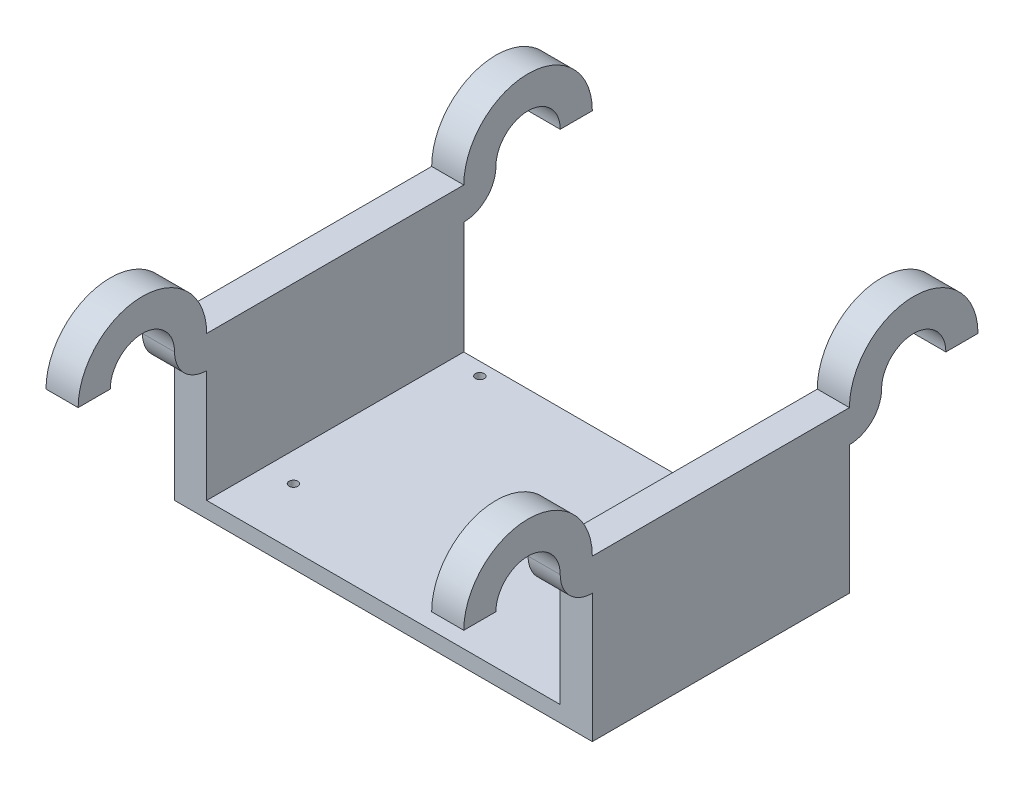
SolidWorks part; units mm, degrees
ref_plane "Front Plane" through (0, 0, 0) normal (0, 0, 1) x (1, 0, 0)
ref_plane "Top Plane" through (0, 0, 0) normal (0, 1, 0) x (1, 0, 0)
ref_plane "Right Plane" through (0, 0, 0) normal (1, 0, 0) x (0, 0, -1)
sketch "Sketch1" plane through (0, 0, 0) normal (0, 1, 0) x (1, 0, 0)
  line L1 (-65, -40) -> (65, -40)
  line L2 (-65, -40) -> (-65, 40)
  line L3 (-65, 40) -> (65, 40)
  line L4 (65, -40) -> (65, 40)
  line L5 (-65, -40) -> (65, 40) construction
  line L6 (-65, 40) -> (65, -40) construction
  point P0 (0, 0)
  dimension "D1" = 130
  dimension "D2" = 80
extrude "Boss-Extrude1" add sketch "Sketch1" along normal blind 5
sketch "Sketch2" plane through (0, 5, 0) normal (0, 1, 0) x (1, 0, 0)
  line L0 (-65, -40) -> (65, -40) construction
  line L1 (65, 40) -> (55, 40)
  line L2 (65, 40) -> (65, -40)
  line L3 (65, -40) -> (55, -40)
  line L4 (55, 40) -> (55, -40)
  line L5 (65, 40) -> (-65, 40) construction
  line L6 (-65, -40) -> (-55, -40)
  line L7 (-65, -40) -> (-65, 40)
  line L8 (-65, 40) -> (-55, 40)
  line L9 (-55, -40) -> (-55, 40)
  dimension "D1" = 10
  dimension "D2" = 10
extrude "Boss-Extrude2" add sketch "Sketch2" along normal blind 45
sketch "Sketch3" plane through (0, 5, 0) normal (0, 1, 0) x (1, 0, 0)
  circle A0 centre (-46, -22) radius 1.375 construction
  circle A1 centre (40, -22) radius 1.375 construction
  circle A2 centre (40, 36) radius 1.375 construction
  circle A3 centre (-46, 36) radius 1.375 construction
  circle A4 centre (-46, -22) radius 1.375
  circle A5 centre (40, -22) radius 1.375
  circle A6 centre (40, 36) radius 1.375
  circle A7 centre (-46, 36) radius 1.375
extrude "Cut-Extrude1" cut sketch "Sketch3" against normal through all both and the other way through all
sketch "Sketch4" plane through (-65, 0, 0) normal (-1, 0, 0) x (0, 0, 1)
  line L0 (0, 0) -> (0, 50) construction
  line L1 (-40, 50) -> (40, 50) construction
  line L2 (-60, 50) -> (60, 50) construction
  line L3 (-70, 50) -> (-40, 50)
  line L4 (70, 50) -> (40, 50)
  line L5 (-80, 50) -> (-70, 50)
  line L6 (80, 50) -> (70, 50)
  line L7 (-40, 50) -> (-40, 0) construction
  line L8 (40, 50) -> (40, 0) construction
  line L9 (-40, 50) -> (-40, 40)
  line L10 (40, 50) -> (40, 40)
  arc A0 (-50, 50) -> (-70, 50) centre (-60, 50) ccw
  arc A1 (70, 50) -> (50, 50) centre (60, 50) ccw
  arc A2 (-40, 50) -> (-80, 50) centre (-60, 50) ccw
  arc A3 (40, 50) -> (80, 50) centre (60, 50) cw
  arc A4 (-50, 50) -> (-40, 40) centre (-40, 50) ccw
  arc A5 (50, 50) -> (40, 40) centre (40, 50) cw
  point P3 (0, 50)
  line M3 (40, 0) -> (40, 50)
  line M5 (-40, 50) -> (-40, 0)
  dimension "D2" = 20
  dimension "D3" = 20
  dimension "D1" = 120
extrude "Boss-Extrude3" add sketch "Sketch4" against normal up to surface (10 mm away) contours L3 A2 L5 A0 | L3 A4 M5 | A3 L4 A1 L6 | A5 L4 M3 up to face at (-55, 27.5, 0)
sketch "Sketch5" plane through (65, 0, 0) normal (1, 0, 0) x (0, 0, -1)
  line L4 (-40, 0) -> (40, 0)
  line L5 (40, 0) -> (40, 50)
  line L6 (40, 50) -> (-40, 50)
  line L7 (-40, 50) -> (-40, 0)
  line L8 (-40, 0) -> (40, 0)
  line L9 (40, 0) -> (40, 50)
  line L10 (40, 50) -> (-40, 50)
  line L11 (-40, 50) -> (-40, 0)
  line L14 (-40, 5) -> (40, 5)
  line L15 (40, 5) -> (40, 40)
  line L16 (70, 50) -> (80, 50)
  line L17 (40, 50) -> (-40, 50)
  line L18 (-80, 50) -> (-70, 50)
  line L19 (-40, 40) -> (-40, 5)
  line L20 (-40, 5) -> (40, 5)
  line L21 (40, 5) -> (40, 40)
  line L22 (70, 50) -> (80, 50)
  line L23 (40, 50) -> (-40, 50)
  line L24 (-80, 50) -> (-70, 50)
  line L25 (-40, 40) -> (-40, 5)
  arc A6 (40, 40) -> (50, 50) centre (40, 50) ccw
  arc A7 (70, 50) -> (50, 50) centre (60, 50) ccw
  arc A8 (80, 50) -> (40, 50) centre (60, 50) ccw
  arc A9 (-40, 50) -> (-80, 50) centre (-60, 50) ccw
  arc A10 (-50, 50) -> (-70, 50) centre (-60, 50) ccw
  arc A11 (-50, 50) -> (-40, 40) centre (-40, 50) ccw
  arc A12 (40, 40) -> (50, 50) centre (40, 50) ccw
  arc A13 (70, 50) -> (50, 50) centre (60, 50) ccw
  arc A14 (80, 50) -> (40, 50) centre (60, 50) ccw
  arc A15 (-40, 50) -> (-80, 50) centre (-60, 50) ccw
  arc A16 (-50, 50) -> (-70, 50) centre (-60, 50) ccw
  arc A17 (-50, 50) -> (-40, 40) centre (-40, 50) ccw
  line M18 (40, 0) -> (40, 50)
  line M20 (-40, 50) -> (-40, 0)
  dimension "D1" = 0
  dimension "D2" = 0
extrude "Boss-Extrude4" add sketch "Sketch5" against normal up to surface (10 mm away) contours A16 A17 A15 L24 M20 | L22 A14 A12 A13 M18 up to face at (55, 27.5, 0)
